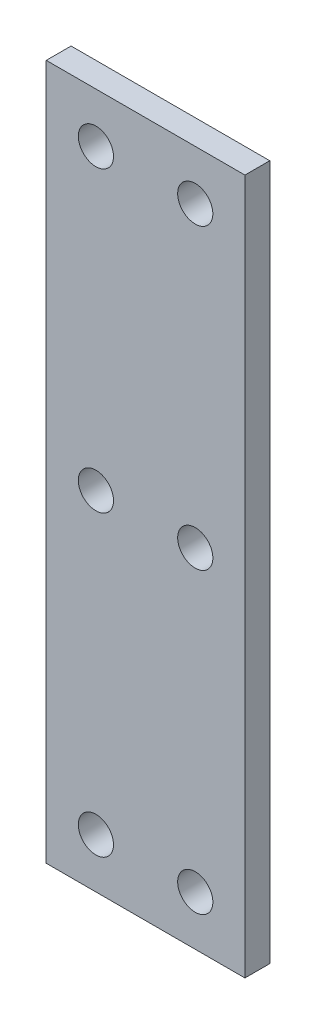
SolidWorks part; units mm, degrees
ref_plane "Front Plane" through (0, 0, 0) normal (0, 0, 1) x (1, 0, 0)
ref_plane "Top Plane" through (0, 0, 0) normal (0, 1, 0) x (1, 0, 0)
ref_plane "Right Plane" through (0, 0, 0) normal (1, 0, 0) x (0, 0, -1)
sketch "Sketch1" plane through (0, 0, 0) normal (0, 0, 1) x (1, 0, 0)
  line L0 (-6.35, 38.1) -> (-6.35, 0) construction
  line L1 (-12.7, -44.45) -> (12.7, -44.45)
  line L2 (-12.7, -44.45) -> (-12.7, 44.45)
  line L3 (-12.7, 44.45) -> (12.7, 44.45)
  line L4 (12.7, -44.45) -> (12.7, 44.45)
  line L5 (-12.7, -44.45) -> (12.7, 44.45) construction
  line L6 (-12.7, 44.45) -> (12.7, -44.45) construction
  line L7 (-6.35, 0) -> (-6.35, -38.1) construction
  line L8 (0, 0) -> (0, -44.45) construction
  circle A0 centre (-6.35, 38.1) radius 2.25
  circle A1 centre (-6.35, 0) radius 2.25
  circle A2 centre (-6.35, -38.1) radius 2.25
  circle A3 centre (6.35, -38.1) radius 2.25
  circle A4 centre (6.35, 0) radius 2.25
  circle A5 centre (6.35, 38.1) radius 2.25
  point P0 (0, 0)
  dimension "D1" = 6.35
  dimension "D3" = 4.5
  dimension "D2" = 38.1
  dimension "D4" = 6.35
  dimension "D5" = 88.9
extrude "Boss-Extrude1" add sketch "Sketch1" along normal blind 3.175
